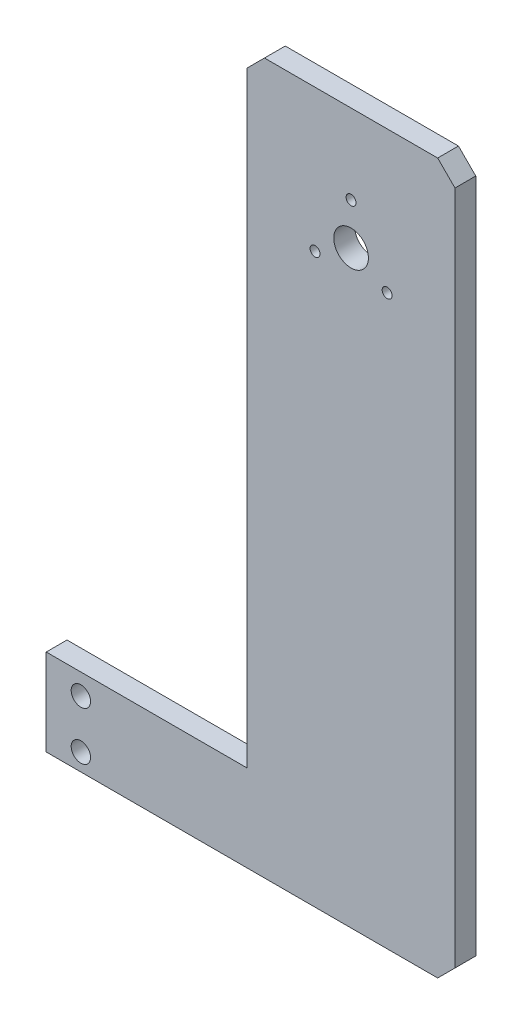
SolidWorks part; units mm, degrees
ref_plane "Front Plane" through (0, 0, 0) normal (0, 0, 1) x (1, 0, 0)
ref_plane "Top Plane" through (0, 0, 0) normal (0, 1, 0) x (1, 0, 0)
ref_plane "Right Plane" through (0, 0, 0) normal (1, 0, 0) x (0, 0, -1)
sketch "Sketch1" plane through (0, 0, 0) normal (0, 0, 1) x (1, 0, 0)
  line L0 (0, 200) -> (0, 5)
  line L1 (-5, 0) -> (-118, 0)
  line L2 (-118, 0) -> (-118, 25)
  line L3 (-118, 25) -> (-60, 25)
  line L4 (-60, 25) -> (-60, 200)
  line L5 (-55, 205) -> (-5, 205)
  line L6 (0, 5) -> (-5, 0)
  line L7 (-5, 205) -> (0, 200)
  line L8 (-60, 200) -> (-55, 205)
  point P0 (0, 205)
  point P1 (0, 0)
  point P7 (-60, 205)
  dimension "D1" = 205
  dimension "D2" = 118
  dimension "D3" = 25
  dimension "D4" = 60
extrude "Boss-Extrude1" add sketch "Sketch1" along normal blind 6
sketch "Sketch2" plane through (0, 0, 6) normal (0, 0, 1) x (1, 0, 0)
  line L0 (-118, 25) -> (-118, 0) construction
  line L1 (-60, 25) -> (-118, 25) construction
  line L9 (-40.4, 163.9956) -> (-19.6, 163.9956) construction
  line L10 (-19.6, 163.9956) -> (-30, 182.0089) construction
  line L11 (-30, 182.0089) -> (-40.4, 163.9956) construction
  line L12 (-5, 205) -> (-55, 205) construction
  circle A0 centre (-108, 19) radius 2.8
  circle A1 centre (-108, 5) radius 2.8
  circle A2 centre (-30, 170) radius 5
  circle A6 centre (-30, 170) radius 6.0044 construction
  circle A7 centre (-19.6, 163.9956) radius 1.43
  circle A8 centre (-40.4, 163.9956) radius 1.43
  circle A9 centre (-30, 182.0089) radius 1.43
  point P17 (0, 0)
  point P18 (0, 0)
  point P21 (-30, 205)
  point P22 (-38.9183, 161.9578)
  point P23 (-19.7396, 164.2343)
  point P24 (0, 0)
  dimension "D1" = 5.6
  dimension "D2" = 10
  dimension "D3" = 6
  dimension "D5" = 20.8
  dimension "D6" = 10
  dimension "D8" = 2.86
  dimension "D4" = 14
  dimension "D7" = 35
extrude "Cut-Extrude1" cut sketch "Sketch2" against normal through all
